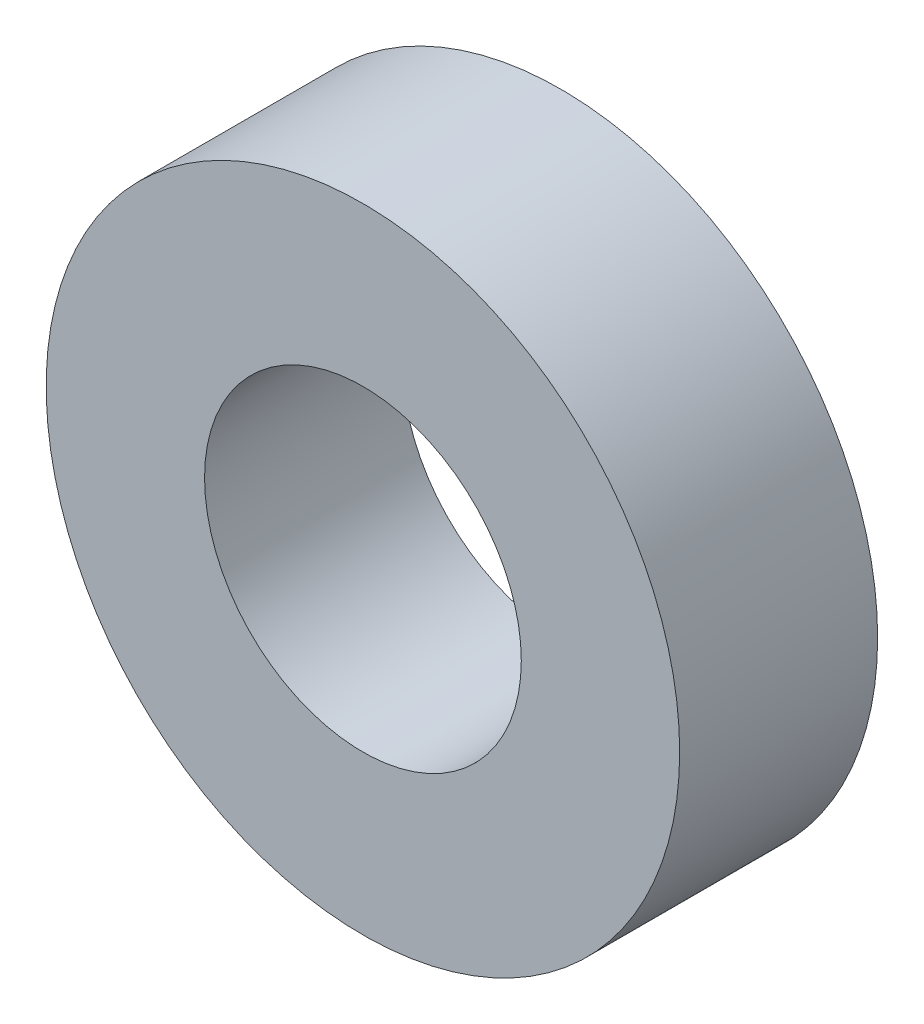
SolidWorks part; units mm, degrees
material "Alloy Steel (SS)"
ref_plane "Front Plane" through (0, 0, 0) normal (0, 0, 1) x (1, 0, 0)
ref_plane "Top Plane" through (0, 0, 0) normal (0, 1, 0) x (1, 0, 0)
ref_plane "Right Plane" through (0, 0, 0) normal (1, 0, 0) x (0, 0, -1)
sketch "Sketch1" plane through (0, 0, 0) normal (0, 0, 1) x (1, 0, 0)
  circle A0 centre (0, 0) radius 8
  circle A1 centre (0, 0) radius 4
  dimension "D1" = 16
  dimension "D2" = 8
extrude "Boss-Extrude1" add sketch "Sketch1" along normal blind 5
